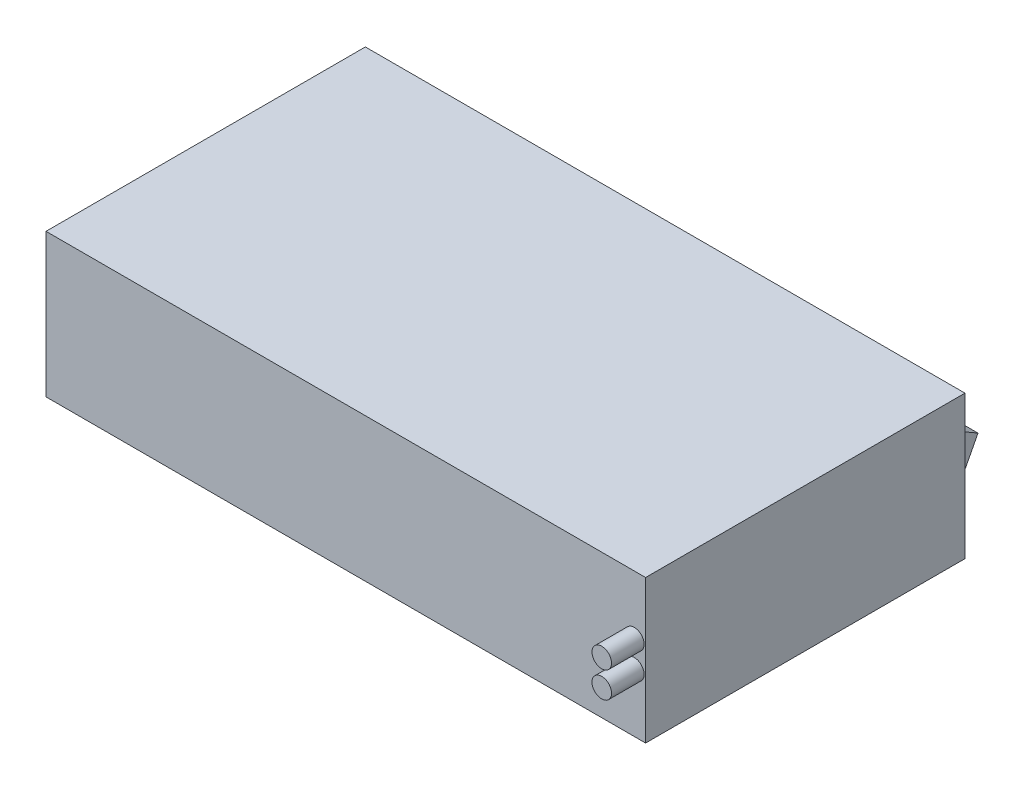
SolidWorks part; units mm, degrees
ref_plane "前视基准面" through (0, 0, 0) normal (0, 0, 1) x (1, 0, 0)
ref_plane "上视基准面" through (0, 0, 0) normal (0, 1, 0) x (1, 0, 0)
ref_plane "右视基准面" through (0, 0, 0) normal (1, 0, 0) x (0, 0, -1)
sketch "草图1" plane through (0, 0, 0) normal (0, 1, 0) x (1, 0, 0)
  line L1 (-47.5452, 34.708) -> (44.4548, 34.708)
  line L2 (-47.5452, 34.708) -> (-47.5452, -14.292)
  line L3 (-47.5452, -14.292) -> (44.4548, -14.292)
  line L4 (44.4548, 34.708) -> (44.4548, -14.292)
  dimension "D1" = 92
  dimension "D2" = 49
extrude "凸台-拉伸1" add sketch "草图1" along normal blind 22
sketch "草图2" plane through (0, 0, -34.708) normal (0, 0, -1) x (-1, 0, 0)
  line L0 (-44.4548, 22) -> (-44.4548, 0) construction
  line L1 (-42.4548, 16) -> (-36.4548, 16)
  line L2 (-42.4548, 16) -> (-42.4548, 6)
  line L3 (-42.4548, 6) -> (-36.4548, 6)
  line L4 (-36.4548, 16) -> (-36.4548, 6)
  line L5 (-44.4548, 22) -> (47.5452, 22) construction
  dimension "D1" = 6
  dimension "D2" = 10
  dimension "D3" = 2
  dimension "D4" = 6
extrude "凸台-拉伸2" add sketch "草图2" along normal blind 4
sketch "草图3" plane through (42.4548, 0, 0) normal (1, 0, 0) x (0, 0, -1)
  line L0 (34.708, 16) -> (34.708, 6)
  line L1 (38.708, 6) -> (34.708, 6) construction
  line L2 (34.708, 16) -> (34.708, 6) construction
  line L3 (34.708, 6) -> (38.708, 13.6906)
  line L4 (38.708, 16) -> (38.708, 6) construction
  line L5 (38.708, 13.6906) -> (34.708, 16)
  line L6 (38.708, 16) -> (34.708, 16) construction
  line L7 (34.708, 16) -> (38.708, 16)
  line L8 (38.708, 16) -> (38.708, 13.6906)
  line L9 (38.708, 6) -> (34.708, 6)
  line M3 (34.708, 6) -> (38.708, 6)
  line M4 (38.708, 6) -> (38.708, 16)
  line M5 (38.708, 16) -> (34.708, 16)
  dimension "D1" = 30
extrude "切除-拉伸2" cut sketch "草图3" against normal through all contours L5 M4 M5 | L3 M3 M4
sketch "草图4" plane through (0, 0, -34.708) normal (0, 0, -1) x (-1, 0, 0)
  line L0 (-44.4548, 22) -> (47.5452, 22) construction
  line L1 (-36.4548, 6) -> (-36.4548, 13.6906) construction
  line L2 (-34.4548, 11) -> (-34.4548, 12)
  line L3 (-34.4548, 11) -> (-34.4548, 10)
  arc A0 (-34.4548, 10) -> (-34.4548, 12) centre (-34.4548, 11) ccw
  dimension "D3" = 2
  dimension "D1" = 11
  dimension "D2" = 2
revolve "旋转1" add sketch "草图4" angle 360 about L2
sketch "草图5" plane through (0, 0, 14.292) normal (0, 0, 1) x (1, 0, 0)
  line L0 (-47.5452, 22) -> (44.4548, 22) construction
  circle A0 centre (42.7266, 13) radius 1.5
  circle A1 centre (42.7266, 9) radius 1.5
  dimension "D1" = 3
  dimension "D2" = 3
  dimension "D3" = 4
  dimension "D4" = 9
extrude "凸台-拉伸3" add sketch "草图5" along normal blind 5
